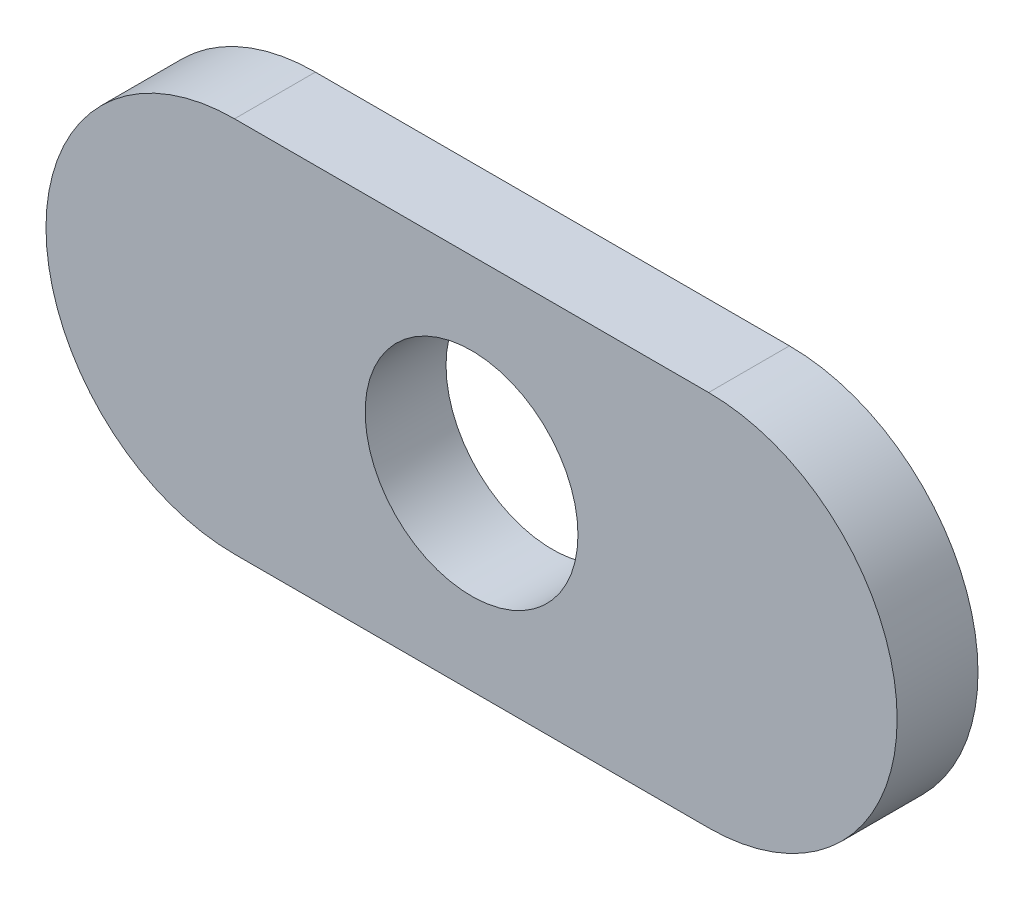
SolidWorks part; units mm, degrees
material "AISI 1020"
ref_plane "Front Plane" through (0, 0, 0) normal (0, 0, 1) x (1, 0, 0)
ref_plane "Top Plane" through (0, 0, 0) normal (0, 1, 0) x (1, 0, 0)
ref_plane "Right Plane" through (0, 0, 0) normal (1, 0, 0) x (0, 0, -1)
sketch "Sketch1" plane through (0, 0, 0) normal (0, 0, 1) x (1, 0, 0)
  line L0 (105.6526, 125.9331) -> (131.0526, 125.9331) construction
  line L88 (111.2787, 131.5592) -> (125.4265, 131.5592)
  line L89 (111.2787, 120.307) -> (125.4265, 120.307)
  arc A0 (111.2787, 120.307) -> (111.2787, 131.5592) centre (111.2787, 125.9331) cw
  arc A1 (125.4265, 120.307) -> (125.4265, 131.5592) centre (125.4265, 125.9331) ccw
  point P4 (105.6526, 125.9331)
  dimension "D1" = 11.2522
  dimension "D2" = 25.4
extrude "Extrude1" add sketch "Sketch1" along normal blind 2.413
sketch "Sketch4" plane through (0, 0, 2.413) normal (0, 0, 1) x (1, 0, 0)
  line L0 (111.2185, 131.5588) -> (125.4866, 131.5588) construction
  line L1 (105.6526, 125.9331) -> (131.0526, 125.9331) construction
  circle A0 centre (118.3526, 125.9331) radius 3.175
  arc A1 (111.2787, 131.5592) -> (111.2787, 120.307) centre (111.2787, 125.9331) ccw construction
  arc A2 (125.4265, 120.307) -> (125.4265, 131.5592) centre (125.4265, 125.9331) ccw construction
  dimension "D1" = 6.35
  dimension "D2" = 7.134
extrude "Cut-Extrude1" cut sketch "Sketch4" against normal up to next
